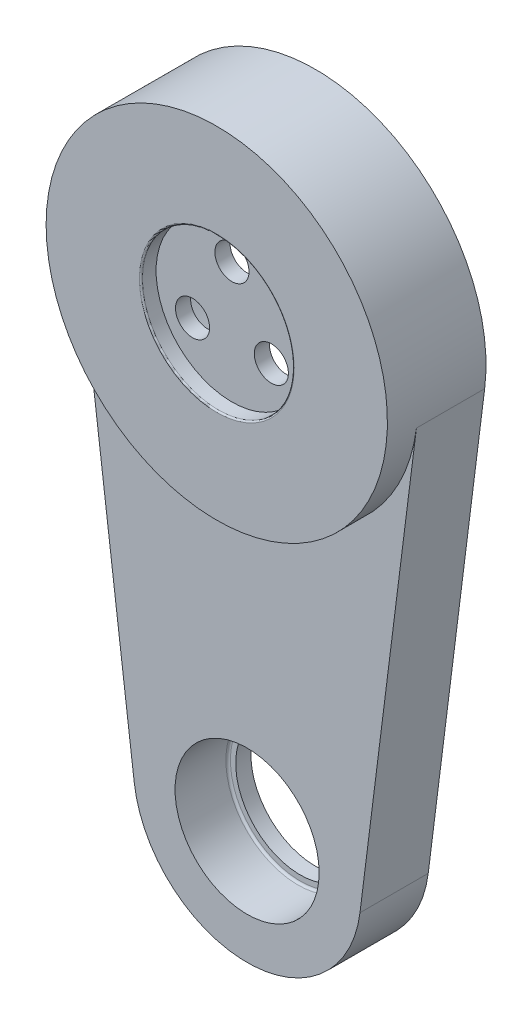
SolidWorks part; units mm, degrees
other "마크업1"
sketch "스케치14" plane through (30, 31, -30.5354) normal (0.2605, 0.9636, -0.0594) x (0.9655, -0.2601, 0.014)
sketch "스케치15" plane through (30, 31, -30.5354) normal (0.2605, 0.9636, -0.0594) x (0.9655, -0.2601, 0.014)
sketch "스케치16" plane through (30, 31, -30.5354) normal (0.2605, 0.9636, -0.0594) x (0.9655, -0.2601, 0.014)
sketch "스케치21" plane through (30, 31, -30.5354) normal (0.2605, 0.9636, -0.0594) x (0.9655, -0.2601, 0.014)
sketch "스케치23" plane through (30, 275, -27) normal (0.2605, 0.9636, -0.0594) x (0.9655, -0.2601, 0.014)
sketch "스케치28" plane through (20, 265, -24) normal (0.2605, 0.9636, -0.0594) x (0.9655, -0.2601, 0.014)
sketch "스케치31" plane through (20, 265, -24) normal (0.2605, 0.9636, -0.0594) x (0.9655, -0.2601, 0.014)
sketch "스케치32" plane through (20, 265, -23) normal (0.2605, 0.9636, -0.0594) x (0.9655, -0.2601, 0.014)
sketch "스케치33" plane through (20, 265, -23) normal (0.2605, 0.9636, -0.0594) x (0.9655, -0.2601, 0.014)
sketch "스케치52" plane through (24, 65, -12) normal (0.2605, 0.9636, -0.0594) x (0.9655, -0.2601, 0.014)
sketch "스케치61" plane through (22.5, 22.5, -13) normal (0.2605, 0.9636, -0.0594) x (0.9655, -0.2601, 0.014)
sketch "스케치64" plane through (22.5, 22.5, -13) normal (0.2605, 0.9636, -0.0594) x (0.9655, -0.2601, 0.014)
sketch "스케치70" plane through (22.5, 22.5, -13) normal (0.2605, 0.9636, -0.0594) x (0.9655, -0.2601, 0.014)
sketch "스케치71" plane through (22.5, 22.5, -13) normal (0.2605, 0.9636, -0.0594) x (0.9655, -0.2601, 0.014)
material "7075-T6 (SN)"
ref_plane "정면" through (0, 0, 0) normal (0, 0, 1) x (1, 0, 0)
ref_plane "윗면" through (0, 0, 0) normal (0, 1, 0) x (1, 0, 0)
ref_plane "우측면" through (0, 0, 0) normal (1, 0, 0) x (0, 0, -1)
sketch "스케치2" plane through (0, 6, 0) normal (0, 0, -1) x (1, 0, 0)
  circle A0 centre (0, 6) radius 22.5
  dimension "D1" = 45
extrude "보스-돌출2" add sketch "스케치2" along normal blind 2
sketch "스케치22" plane through (0, 0, 0) normal (0, 0, 1) x (1, 0, 0)
  circle A0 centre (0, 0) radius 10
  dimension "D1" = 20
extrude "컷-돌출1" cut sketch "스케치22" against normal blind 2 contours A0
fillet "필렛4" radius 0.2 1 edges at (10, 0, 0)
sketch "스케치54" plane through (0, 0, -2) normal (0, 0, -1) x (-1, 0, 0)
  circle A4 centre (0, 0) radius 22.5 construction
  circle A5 centre (0, 0) radius 22.5
extrude "보스-돌출6" add sketch "스케치54" along normal blind 11
sketch "스케치55" plane through (0, 0, -13) normal (0, 0, -1) x (-1, 0, 0)
  circle A0 centre (0, 0) radius 18.5
  dimension "D1" = 37
extrude "컷-돌출2" cut sketch "스케치55" against normal blind 8
sketch "스케치56" plane through (0, 0, -5) normal (0, 0, -1) x (-1, 0, 0)
  circle A0 centre (0, 0) radius 6 construction
  point P3 (0, 6)
  dimension "D1" = 12
hole_wizard "M4 육각 소켓 머리 캡 나사용 카운터보어1" positions "스케치57" profile "스케치58" counterbore size "M4" standard "ISO" end condition through all
sketch "스케치57" plane through (0, 0, -5) normal (0, 0, -1) x (-1, 0, 0)
  point P0 (0, 6)
sketch "스케치58" plane through (0, 6, -5) normal (1, 0, 0) x (0, 1, 0)
  line L0 (0, 0) -> (0, 5)
  line L1 (0, 5) -> (2.25, 5)
  line L3 (2.25, 5) -> (2.25, 1)
  line L4 (2.25, 1) -> (4, 1)
  line L5 (4, 1) -> (4, 0)
  line L7 (4, 0) -> (0, 0)
  line L11 (0, -6.35) -> (0, 107.95) construction
  dimension "관통 구멍 지름" = 4.5
  dimension "관통 구멍 깊이" = 5
  dimension "카운터보어 지름" = 8
  dimension "카운터보어 깊이" = 1
pattern_circular "원형 패턴1" count 3 over 360 about axis through (0, 0, 0) along (0, 0, 1) of "M4 육각 소켓 머리 캡 나사용 카운터보어1"
sketch "스케치59" plane through (0, 0, -5) normal (0, 0, -1) x (-1, 0, 0)
  circle A0 centre (0, 0) radius 17.5
  circle A1 centre (0, 0) radius 18.5 construction
  circle A2 centre (0, 0) radius 18.5
  dimension "D1" = 35
extrude "보스-돌출7" add sketch "스케치59" along normal blind 1
sketch "스케치60" plane through (0, 0, -13) normal (0, 0, -1) x (-1, 0, 0)
  line L0 (-22.3235, -2.8125) -> (-14.8824, -61.875)
  line L1 (0, 0) -> (0, -60) construction
  line L2 (22.3235, -2.8125) -> (14.8824, -61.875)
  circle A0 centre (0, 0) radius 22.5 construction
  arc A1 (-14.8824, -61.875) -> (14.8824, -61.875) centre (0, -60) ccw
  arc A2 (-22.3235, -2.8125) -> (22.3235, -2.8125) centre (0, 0) ccw
  dimension "D2" = 30
  dimension "D1" = 60
extrude "보스-돌출8" add sketch "스케치60" against normal blind 9
fillet "필렛6" radius 0.3 1 edges at (-18.5, 0, -6)
sketch "스케치68" plane through (0, 0, -4) normal (0, 0, 1) x (1, 0, 0)
  circle A0 centre (0, -60) radius 9.5
  dimension "D1" = 19
extrude "컷-돌출7" cut sketch "스케치68" against normal blind 7
sketch "스케치69" plane through (0, 0, -11) normal (0, 0, 1) x (1, 0, 0)
  circle A0 centre (0, -60) radius 8.5
  dimension "D1" = 17
extrude "컷-돌출8" cut sketch "스케치69" against normal through all
fillet "필렛7" radius 0.3 1 edges at (9.5, -60, -11)
